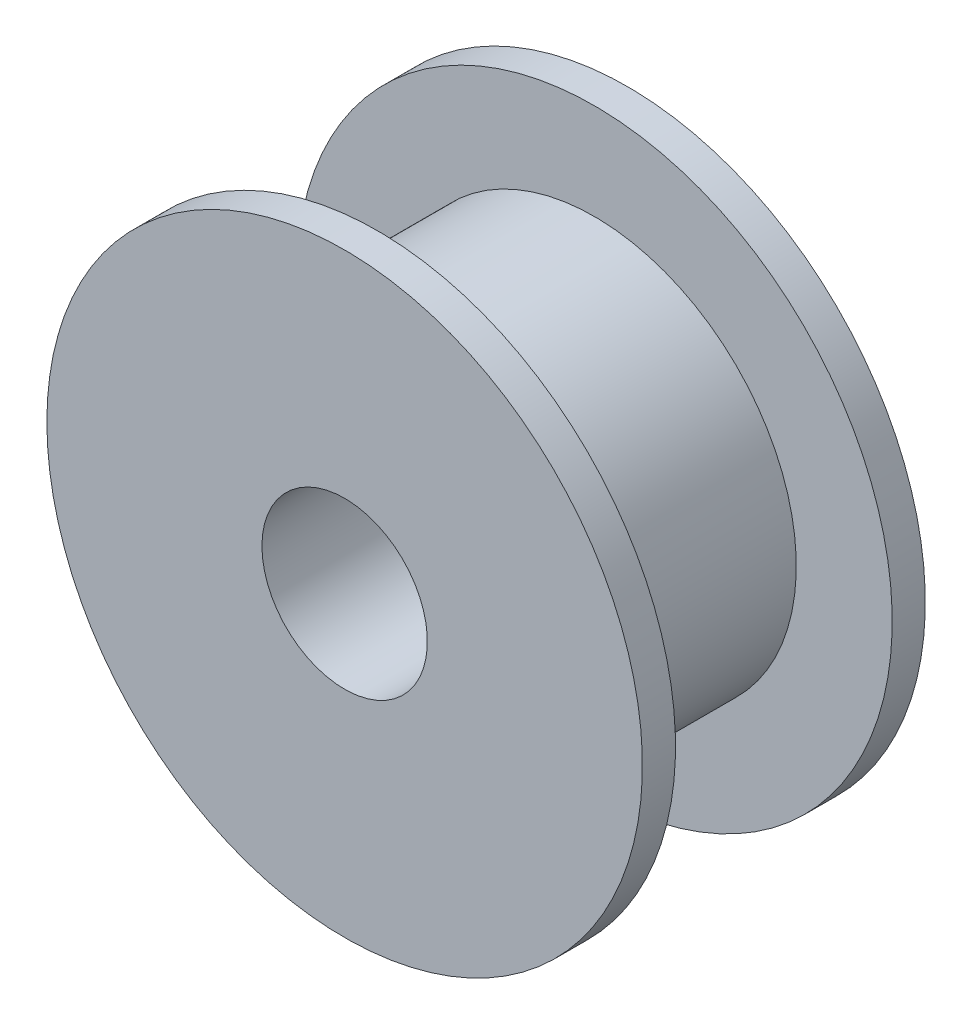
SolidWorks part; units mm, degrees
ref_plane "Front Plane" through (0, 0, 0) normal (0, 0, 1) x (1, 0, 0)
ref_plane "Top Plane" through (0, 0, 0) normal (0, 1, 0) x (1, 0, 0)
ref_plane "Right Plane" through (0, 0, 0) normal (1, 0, 0) x (0, 0, -1)
sketch "Sketch2" plane through (0, 0, 0) normal (0, 1, 0) x (1, 0, 0)
  line L0 (-9, 4.275) -> (-2.5, 4.275)
  line L1 (-2.5, 4.275) -> (-2.5, -4.275)
  line L2 (-2.5, -4.275) -> (-9, -4.275)
  line L3 (-9, -4.275) -> (-9, -3.275)
  line L4 (-9, -3.275) -> (-6.1, -3.275)
  line L5 (-6.1, -3.275) -> (-6.1, 3.275)
  line L6 (-6.1, 3.275) -> (-9, 3.275)
  line L7 (-9, 3.275) -> (-9, 4.275)
  line L8 (0, 4.275) -> (0, -4.275) construction
  line L9 (9, 3.275) -> (9, 4.275) construction
  line L10 (6.1, 3.275) -> (9, 3.275) construction
  line L11 (6.1, -3.275) -> (6.1, 3.275) construction
  line L12 (9, -3.275) -> (6.1, -3.275) construction
  line L13 (9, -4.275) -> (9, -3.275) construction
  line L14 (2.5, -4.275) -> (9, -4.275) construction
  line L15 (2.5, 4.275) -> (2.5, -4.275) construction
  line L16 (9, 4.275) -> (2.5, 4.275) construction
  point P11 (0, 0)
  dimension "D1" = 1
  dimension "D2" = 8.55
  dimension "D3" = 12.2
  dimension "D4" = 18
  dimension "D5" = 5
revolve "Revolve1" add sketch "Sketch2" angle 360 about L8
